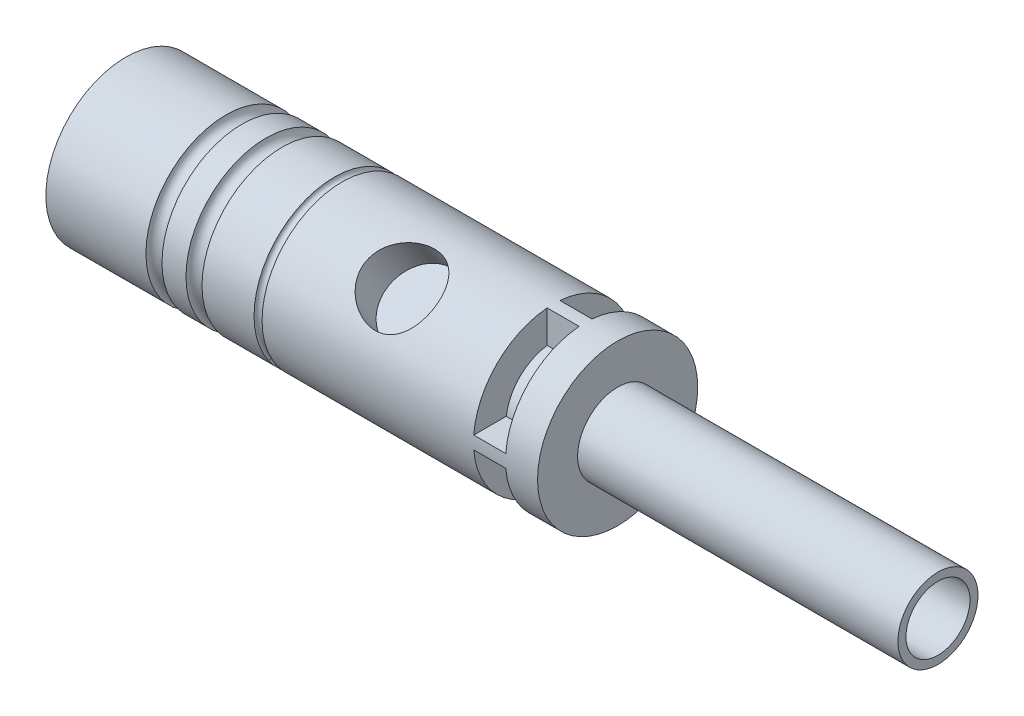
SolidWorks part; units mm, degrees
material "6061-T6 (SS)"
ref_plane "Front Plane" through (0, 0, 0) normal (0, 0, 1) x (1, 0, 0)
ref_plane "Top Plane" through (0, 0, 0) normal (0, 1, 0) x (1, 0, 0)
ref_plane "Right Plane" through (0, 0, 0) normal (1, 0, 0) x (0, 0, -1)
sketch "Sketch1" plane through (0, 0, 0) normal (1, 0, 0) x (0, 0, -1)
  circle A0 centre (0, 0) radius 12.7
  dimension "D1" = 25.4
extrude "Boss-Extrude1" add sketch "Sketch1" along normal mid plane 77.978
sketch "Sketch2" plane through (38.989, 0, 0) normal (1, 0, 0) x (0, 0, -1)
  circle A0 centre (0, 0) radius 6.35
  dimension "D1" = 12.7
extrude "Boss-Extrude2" add sketch "Sketch2" along normal blind 50.8
sketch "Sketch3" plane through (0, 0, 0) normal (0, 1, 0) x (1, 0, 0)
  line L0 (-39.0343, 0) -> (89.789, 0) construction
  line L1 (-16.98, 0) -> (16.98, 0) construction
  line L2 (89.789, -6.35) -> (89.789, 6.35) construction
sketch "Sketch4" plane through (0, 0, 0) normal (0, 1, 0) x (1, 0, 0)
  line L0 (-39.0343, 0) -> (89.789, 0) construction
  circle A0 centre (-21.8893, 0) radius 3.175
  dimension "D1" = 6.35
  dimension "D2" = 17.145
sketch "Sketch5" plane through (89.789, 0, 0) normal (1, 0, 0) x (0, 0, -1)
  circle A0 centre (0, 0) radius 5.08
  dimension "D1" = 10.16
extrude "Cut-Extrude1" cut sketch "Sketch5" against normal blind 50.8
sketch "Sketch6" plane through (-38.989, 0, 0) normal (-1, 0, 0) x (0, 0, 1)
  circle A0 centre (0, 0) radius 11.938
  dimension "D1" = 23.876
extrude "Cut-Extrude2" cut sketch "Sketch6" against normal blind 11.684
sketch "Sketch7" plane through (-27.305, 0, 0) normal (-1, 0, 0) x (0, 0, 1)
  circle A0 centre (0, 0) radius 1.27
  dimension "D1" = 2.54
extrude "Boss-Extrude4" add sketch "Sketch7" along normal blind 6.35
ref_plane "Plane1" through (0, 0, 0) normal (0, -0.8988, -0.4384) x (1, 0, 0)
ref_plane "Plane2" through (0, 11.4147, 5.5673) normal (0, 0.8988, 0.4384) x (-1, 0, 0)
sketch "Sketch8" plane through (0, 11.4147, 5.5673) normal (0, 0.8988, 0.4384) x (-1, 0, 0)
  line L0 (38.989, -12.7) -> (38.989, 12.7) construction
  circle A0 centre (-7.4423, 3.7433) radius 4.699
  dimension "D1" = 9.398
  dimension "D2" = 46.4313
ref_plane "Plane3" through (0, 0, 0) normal (0, 0.4384, -0.8988) x (-1, 0, 0)
ref_plane "Plane4" through (0, 5.5673, -11.4147) normal (0, 0.4384, -0.8988) x (-1, 0, 0)
sketch "Sketch9" plane through (0, 5.5673, -11.4147) normal (0, 0.4384, -0.8988) x (-1, 0, 0)
  line L0 (39.0343, 0) -> (-89.789, 0) construction
  line L1 (38.989, -12.7) -> (38.989, 12.7) construction
  circle A0 centre (15.1892, 0) radius 2.032
  circle A1 centre (-14.8336, 0) radius 2.032
  dimension "D1" = 4.064
  dimension "D2" = 25.9588
  dimension "D3" = 21.7678
sketch "Sketch10" plane through (0, 11.5288, 8.0016) normal (0, 0.8215, 0.5702) x (1, 0, 0)
  circle A0 centre (11.732, 0) radius 5.715
  dimension "D1" = 11.43
extrude "Cut-Extrude3" cut sketch "Sketch10" against normal blind 7.62
sketch "Sketch11" plane through (0, 0, 0) normal (0, -0.5702, 0.8215) x (1, 0, 0)
  circle A0 centre (16.024, 0) radius 2.3066
  circle A1 centre (-9.8734, 0) radius 2.3066
extrude "Cut-Extrude4" cut sketch "Sketch11" against normal through all
ref_plane "Plane5" through (33.909, 0, 0) normal (1, 0, 0) x (0, 0, -1)
sketch "Sketch12" [suppressed] plane through (33.909, 0, 0) normal (1, 0, 0) x (0, 0, -1)
  line L1 (0.762, -12.6771) -> (0.762, -12.7)
  line L2 (0.762, 12.7) -> (0.762, 7.9015)
  line L3 (7.9015, 0.762) -> (12.7, 0.762)
  line L6 (-12.6771, -0.762) -> (-12.7, -0.762)
  line L9 (-0.762, 7.9015) -> (-0.762, 12.7)
  line L10 (-12.7, 0.762) -> (-7.9015, 0.762)
  line L11 (-0.762, -12.7) -> (-0.762, -7.9015)
  line L12 (12.7, -0.762) -> (7.9015, -0.762)
  arc A1 (7.9015, 0.762) -> (0.762, 7.9015) centre (0, 0) ccw
  arc A2 (12.6771, 0.762) -> (0.762, 12.6771) centre (0, 0) ccw
  arc A9 (-0.762, 12.6771) -> (-12.6771, 0.762) centre (0, 0) ccw
  arc A10 (-0.762, 7.9015) -> (-7.9015, 0.762) centre (0, 0) ccw
  arc A11 (-12.6771, -0.762) -> (-0.762, -12.6771) centre (0, 0) ccw
  arc A12 (-7.9015, -0.762) -> (-0.762, -7.9015) centre (0, 0) ccw
  arc A13 (0.762, -7.9015) -> (7.9015, -0.762) centre (0, 0) ccw
  arc A14 (0.762, -12.6771) -> (12.6771, -0.762) centre (0, 0) ccw
  dimension "D1" = 4
sketch "Sketch13" plane through (33.909, 0, 0) normal (1, 0, 0) x (0, 0, -1)
  line L0 (0, 0) -> (0, 13.544) construction
  line L1 (0, 0) -> (13.544, 0) construction
  line L2 (1.016, 7.5067) -> (1.016, 13.5058)
  line L3 (13.5058, 1.016) -> (7.5067, 1.016)
  arc A0 (7.5067, 1.016) -> (1.016, 7.5067) centre (0, 0) ccw
  arc A1 (13.5058, 1.016) -> (1.016, 13.5058) centre (0, 0) ccw
  dimension "D1" = 1.016
  dimension "D2" = 1.016
extrude "Cut-Extrude5" cut sketch "Sketch13" against normal blind 5.08
pattern_circular "CirPattern1" count 4 over 360 about axis through (0, 0, 0) along (1, 0, 0) of "Cut-Extrude5"
sketch "Sketch14" plane through (0, 0, 0) normal (0, 0, 1) x (1, 0, 0)
  line L0 (38.989, 12.7) -> (-38.989, 12.7) construction
  line L2 (-38.989, 12.7) -> (-38.989, -12.7) construction
  circle A0 centre (-21.844, 12.7) radius 1.27
  circle A1 centre (-15.494, 12.7) radius 1.27
  circle A2 centre (-5.334, 12.7) radius 0.635
  dimension "D1" = 2.54
  dimension "D2" = 2.54
  dimension "D3" = 1.27
  dimension "D4" = 17.145
  dimension "D5" = 6.35
  dimension "D6" = 10.16
revolve "Cut-Revolve1" cut sketch "Sketch14" angle 360 about L0
